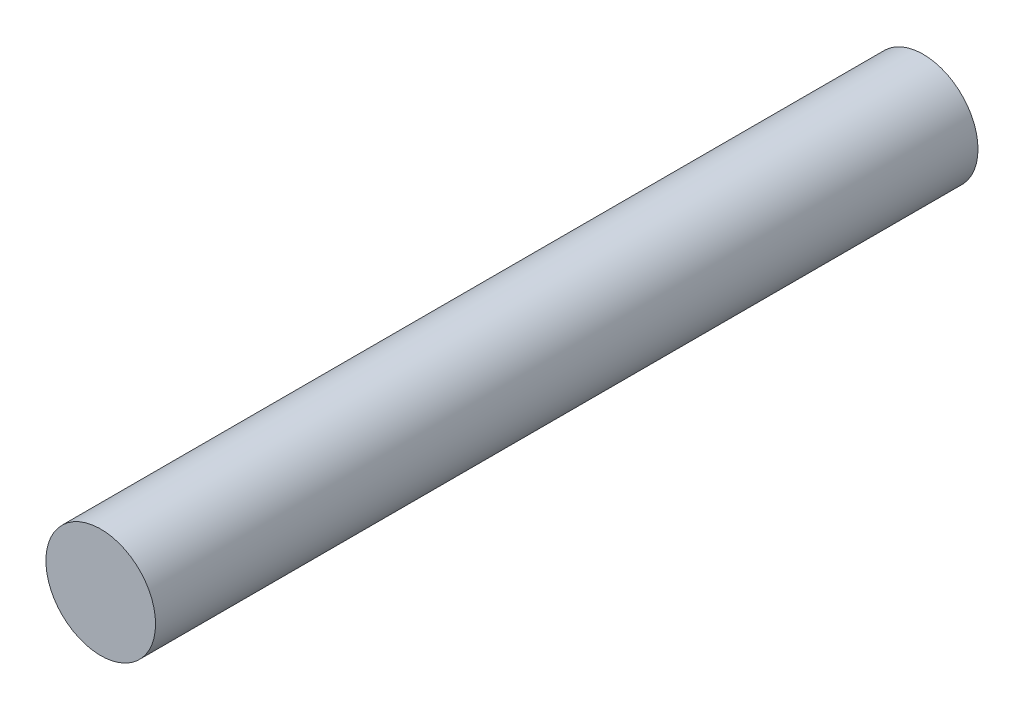
SolidWorks part; units mm, degrees
ref_plane "Front Plane" through (0, 0, 0) normal (0, 0, 1) x (1, 0, 0)
ref_plane "Top Plane" through (0, 0, 0) normal (0, 1, 0) x (1, 0, 0)
ref_plane "Right Plane" through (0, 0, 0) normal (1, 0, 0) x (0, 0, -1)
sketch "Sketch1" plane through (0, 0, 0) normal (0, 0, 1) x (1, 0, 0)
  circle A0 centre (0, 0) radius 2
  dimension "D1" = 4
extrude "Boss-Extrude1" add sketch "Sketch1" along normal blind 30
